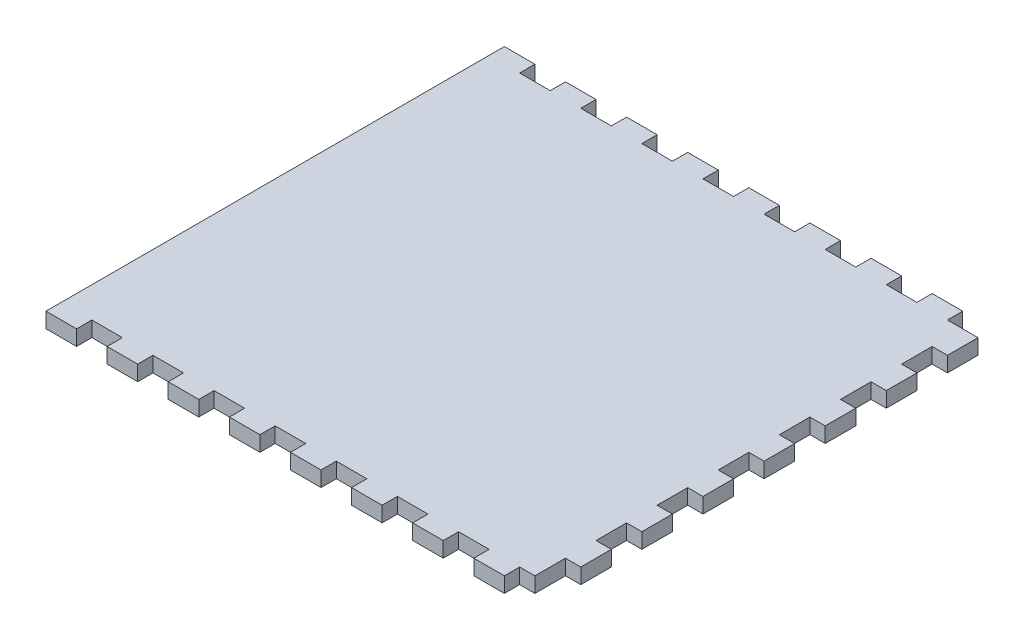
SolidWorks part; units mm, degrees
ref_plane "Front Plane" through (0, 0, 0) normal (0, 0, 1) x (1, 0, 0)
ref_plane "Top Plane" through (0, 0, 0) normal (0, 1, 0) x (1, 0, 0)
ref_plane "Right Plane" through (0, 0, 0) normal (1, 0, 0) x (0, 0, -1)
sketch "Sketch1" plane through (0, 0, 0) normal (0, 1, 0) x (1, 0, 0)
  line L1 (-101.6, -95.25) -> (101.6, -95.25)
  line L2 (-101.6, -95.25) -> (-101.6, 95.25)
  line L3 (-101.6, 95.25) -> (101.6, 95.25)
  line L4 (101.6, -95.25) -> (101.6, 95.25)
  line L5 (-101.6, -95.25) -> (101.6, 95.25) construction
  line L6 (-101.6, 95.25) -> (101.6, -95.25) construction
  point P0 (0, 0)
  point P10 (0, 0)
  point P11 (0, 0)
  dimension "D1" = 190.5
  dimension "D2" = 203.2
extrude "Boss-Extrude1" add sketch "Sketch1" along normal blind 6.35
sketch "Sketch2" plane through (0, 0, 0) normal (0, -1, 0) x (1, 0, 0)
  line L0 (-101.6, 95.25) -> (101.6, 95.25) construction
  line L1 (-88.9, 95.25) -> (-76.2, 95.25)
  line L2 (-88.9, 95.25) -> (-88.9, 88.9)
  line L3 (-88.9, 88.9) -> (-76.2, 88.9)
  line L4 (-76.2, 95.25) -> (-76.2, 88.9)
  dimension "D1" = 6.35
  dimension "D2" = 12.7
  dimension "D3" = 12.7
extrude "Cut-Extrude1" cut sketch "Sketch2" against normal through all
pattern_linear "LPattern1" count 8 spacing 25.4 along (1, 0, 0) of "Cut-Extrude1"
mirror "Mirror1" about plane through (0, 0, 0) normal (0, 0, 1) of "LPattern1", "Cut-Extrude1"
sketch "Sketch4" plane through (0, 6.35, 0) normal (0, 1, 0) x (1, 0, 0)
  line L0 (101.6, -88.9) -> (101.6, 88.9) construction
  line L1 (101.6, 76.2) -> (95.25, 76.2)
  line L2 (101.6, 76.2) -> (101.6, 63.5)
  line L3 (101.6, 63.5) -> (95.25, 63.5)
  line L4 (95.25, 76.2) -> (95.25, 63.5)
  dimension "D1" = 6.35
  dimension "D2" = 12.7
  dimension "D3" = 12.7
extrude "Cut-Extrude2" cut sketch "Sketch4" against normal through all
pattern_linear "LPattern2" count 7 spacing 25.4 along (0, 0, 1) of "Cut-Extrude2"
